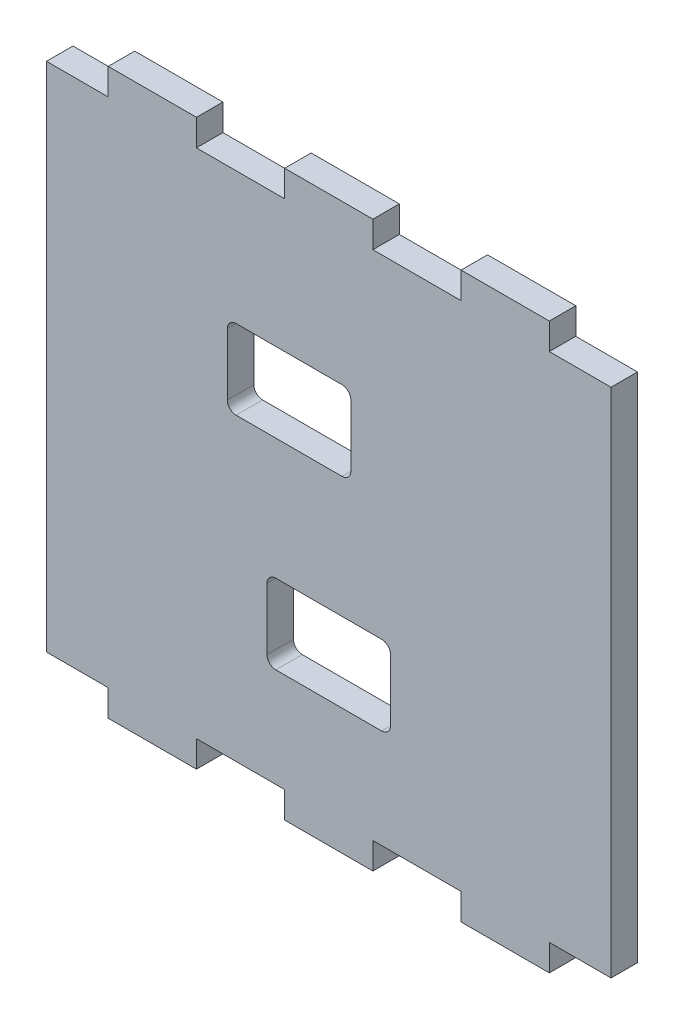
SolidWorks part; units mm, degrees
ref_plane "Alzado" through (0, 0, 0) normal (0, 0, 1) x (1, 0, 0)
ref_plane "Planta" through (0, 0, 0) normal (0, 1, 0) x (1, 0, 0)
ref_plane "Vista lateral" through (0, 0, 0) normal (1, 0, 0) x (0, 0, -1)
sketch "Croquis1" plane through (0, 0, 0) normal (0, 0, 1) x (1, 0, 0)
  line L0 (-32, 29) -> (-25, 29)
  line L2 (-32, -29) -> (-32, 29)
  line L4 (32, -29) -> (32, 29)
  line L5 (-32, -29) -> (32, 29) construction
  line L6 (-32, 29) -> (32, -29) construction
  line L7 (-25, 29) -> (-25, 32)
  line L8 (-25, 32) -> (-15, 32)
  line L9 (-15, 32) -> (-15, 29)
  line L10 (-15, 29) -> (-5, 29)
  line L11 (-5, 29) -> (-5, 32)
  line L12 (-5, 32) -> (5, 32)
  line L13 (5, 32) -> (5, 29)
  line L14 (5, 29) -> (15, 29)
  line L15 (15, 29) -> (15, 32)
  line L16 (15, 32) -> (25, 32)
  line L17 (25, 32) -> (25, 29)
  line L18 (25, 29) -> (32, 29)
  line L19 (-32, -29) -> (-25, -29)
  line L20 (-25, -29) -> (-25, -32)
  line L21 (-25, -32) -> (-15, -32)
  line L22 (-15, -32) -> (-15, -29)
  line L23 (-15, -29) -> (-5, -29)
  line L24 (-5, -29) -> (-5, -32)
  line L25 (-5, -32) -> (5, -32)
  line L26 (5, -32) -> (5, -29)
  line L27 (5, -29) -> (15, -29)
  line L28 (15, -29) -> (15, -32)
  line L29 (15, -32) -> (25, -32)
  line L30 (25, -32) -> (25, -29)
  line L31 (25, -29) -> (32, -29)
  point P0 (0, 0)
  dimension "D1" = 58
  dimension "D2" = 10
  dimension "D3" = 10
  dimension "D4" = 64
  dimension "D5" = 3
extrude "Saliente-Extruir1" add sketch "Croquis1" along normal blind 3
sketch "Croquis2" plane through (0, 0, 3) normal (0, 0, 1) x (1, 0, 0)
  line L0 (0, 0) -> (0, -13.25) construction
  line L1 (-7, -8.75) -> (7, -8.75)
  line L2 (-7, -8.75) -> (-7, -17.75)
  line L3 (-7, -17.75) -> (7, -17.75)
  line L4 (7, -8.75) -> (7, -17.75)
  line L5 (-7, -8.75) -> (7, -17.75) construction
  line L6 (-7, -17.75) -> (7, -8.75) construction
  line L7 (-11.5, 14) -> (2.5, 14)
  line L8 (-11.5, 14) -> (-11.5, 5)
  line L9 (-11.5, 5) -> (2.5, 5)
  line L10 (2.5, 14) -> (2.5, 5)
  line L11 (-11.5, 14) -> (2.5, 5) construction
  line L12 (-11.5, 5) -> (2.5, 14) construction
  line L13 (0, 0) -> (0, 9.5) construction
  line L14 (0, 9.5) -> (-4.5, 9.5) construction
  line L15 (-5, 29) -> (-15, 29) construction
  line L16 (5, -29) -> (15, -29) construction
  point P0 (0, -13.25)
  point P5 (-4.5, 9.5)
  dimension "D1" = 15
  dimension "D2" = 11.25
  dimension "D3" = 4.5
  dimension "D4" = 14
  dimension "D5" = 9
  dimension "D6" = 14
  dimension "D7" = 9
extrude "Cortar-Extruir1" cut sketch "Croquis2" against normal blind 3
fillet "Redondeo1" radius 1 8 edges at (7, -17.75, 1.5) (7, -8.75, 1.5) (-7, -17.75, 1.5) (-7, -8.75, 1.5) (-11.5, 5, 1.5) (2.5, 5, 1.5) (2.5, 14, 1.5) (-11.5, 14, 1.5)
